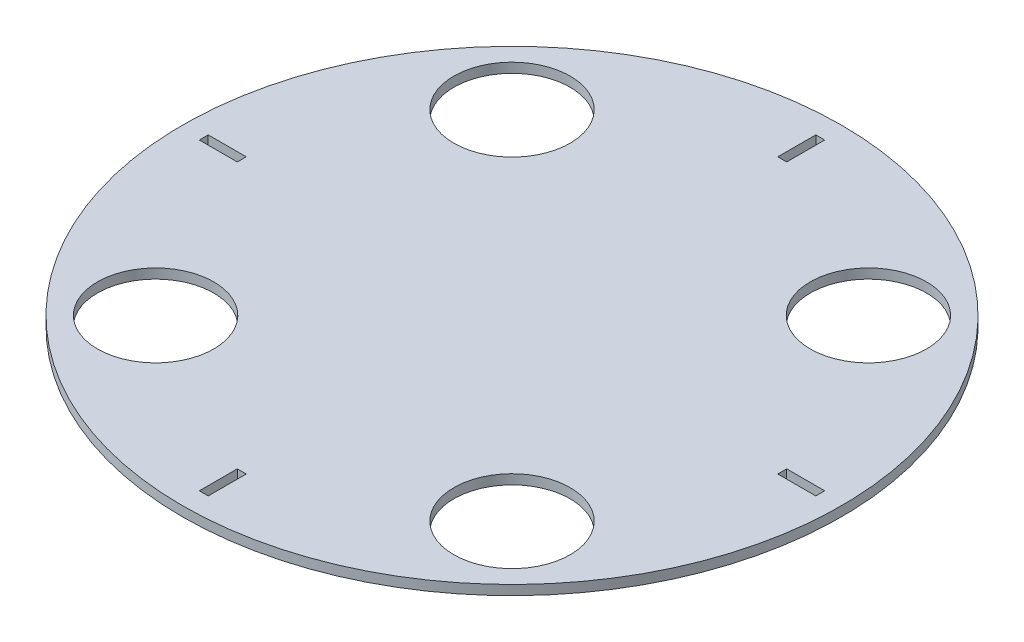
SolidWorks part; units mm, degrees
ref_plane "Front Plane" through (0, 0, 0) normal (0, 0, 1) x (1, 0, 0)
ref_plane "Top Plane" through (0, 0, 0) normal (0, 1, 0) x (1, 0, 0)
ref_plane "Right Plane" through (0, 0, 0) normal (1, 0, 0) x (0, 0, -1)
sketch "Sketch1" plane through (0, 0, 0) normal (0, 1, 0) x (1, 0, 0)
  line L0 (0, -1000) -> (0, 49000) construction
  line L1 (-1000, 0) -> (49000, 0) construction
  line L2 (0, 0) -> (76.3322, 76.3322) construction
  line L3 (0, 0) -> (76.3322, -76.3322) construction
  line L4 (0, 0) -> (-76.3322, -76.3322) construction
  line L5 (0, 0) -> (-76.3322, 76.3322) construction
  line L6 (1.4605, -100.965) -> (1.4605, -88.519)
  line L7 (100.965, 1.4605) -> (88.519, 1.4605)
  line L8 (100.965, 1.4605) -> (100.965, -1.4605)
  line L9 (100.965, -1.4605) -> (88.519, -1.4605)
  line L10 (88.519, 1.4605) -> (88.519, -1.4605)
  line L11 (1.4605, -100.965) -> (-1.4605, -100.965)
  line L12 (-1.4605, -100.965) -> (-1.4605, -88.519)
  line L13 (1.4605, -88.519) -> (-1.4605, -88.519)
  line L14 (-100.965, -1.4605) -> (-88.519, -1.4605)
  line L15 (-100.965, -1.4605) -> (-100.965, 1.4605)
  line L16 (-100.965, 1.4605) -> (-88.519, 1.4605)
  line L17 (-88.519, -1.4605) -> (-88.519, 1.4605)
  line L18 (-1.4605, 100.965) -> (-1.4605, 88.519)
  line L19 (-1.4605, 100.965) -> (1.4605, 100.965)
  line L20 (1.4605, 100.965) -> (1.4605, 88.519)
  line L21 (-1.4605, 88.519) -> (1.4605, 88.519)
  circle A0 centre (0, 0) radius 107.95
  circle A1 centre (58.3717, 58.3717) radius 19.05
  circle A2 centre (58.3717, -58.3717) radius 19.05
  circle A3 centre (-58.3717, -58.3717) radius 19.05
  circle A4 centre (-58.3717, 58.3717) radius 19.05
  point P13 (0, 0)
  point P22 (0, 0)
  point P25 (107.95, 0)
  point P41 (-3.175, 0)
  point P42 (0.381, 0)
  point P43 (0, 0)
  dimension "D1" = 215.9
  dimension "D4" = 38.1
  dimension "D2" = 45
  dimension "D5" = 25.4
  dimension "D7" = 2.921
  dimension "D8" = 1.4605
  dimension "D9" = 12.446
  dimension "D10" = 6.985
  dimension "D3" = 4
  dimension "D6" = 4
extrude "Boss-Extrude1" add sketch "Sketch1" against normal blind 3.175
